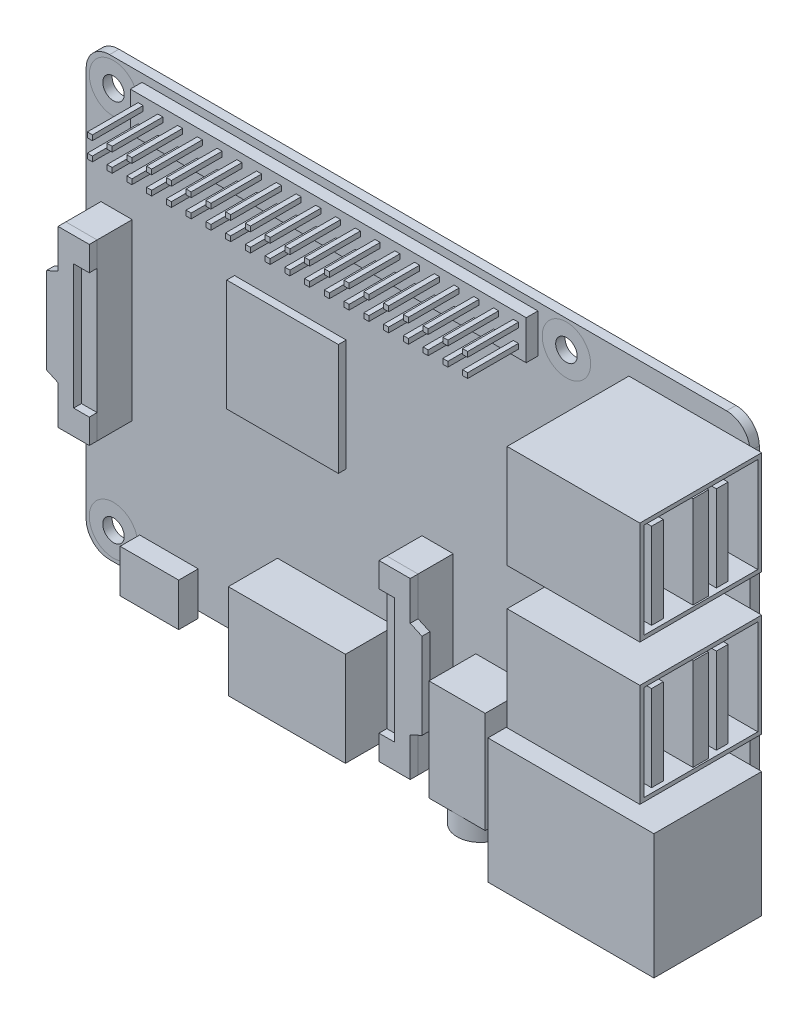
SolidWorks part; units mm, degrees
ref_plane "Ebene vorne" through (0, 0, 0) normal (0, 0, 1) x (1, 0, 0)
ref_plane "Ebene oben" through (0, 0, 0) normal (0, 1, 0) x (1, 0, 0)
ref_plane "Ebene rechts" through (0, 0, 0) normal (1, 0, 0) x (0, 0, -1)
sketch "Skizze1" plane through (0, 0, 0) normal (0, 0, 1) x (1, 0, 0)
  line L1 (42.5, -28) -> (-42.5, -28)
  line L2 (42.5, -28) -> (42.5, 28)
  line L3 (42.5, 28) -> (-42.5, 28)
  line L4 (-42.5, -28) -> (-42.5, 28)
  line L5 (42.5, -28) -> (-42.5, 28) construction
  line L6 (42.5, 28) -> (-42.5, -28) construction
  point P0 (0, 0)
  dimension "D1" = 85
  dimension "D2" = 56
extrude "Aufsatz-Linear austragen1" add sketch "Skizze1" along normal blind 1.2
fillet "Verrundung1" radius 3 4 edges at (-42.5, 28, 0.6) (-42.5, -28, 0.6) (42.5, -28, 0.6) (42.5, 28, 0.6)
sketch "Skizze2" plane through (0, 0, 1.2) normal (0, 0, 1) x (1, 0, 0)
  line L0 (-42.5, 25) -> (-42.5, -25) construction
  line L1 (39.5, 28) -> (-39.5, 28) construction
  line L2 (-39.5, -28) -> (39.5, -28) construction
  circle A0 centre (-39, 24.5) radius 1.375
  circle A1 centre (-39, -24.5) radius 1.375
  circle A2 centre (19, 24.5) radius 1.375
  circle A3 centre (19, -24.5) radius 1.375
  dimension "D4" = 2.75
  dimension "D1" = 3.5
  dimension "D2" = 3.5
  dimension "D3" = 3.5
  dimension "D5" = 58
extrude "Schnitt-Linear austragen1" cut sketch "Skizze2" against normal blind 5
sketch "Skizze3" plane through (0, 0, 1.2) normal (0, 0, 1) x (1, 0, 0)
  circle A0 centre (-39, 24.5) radius 3.1
  circle A1 centre (-39, -24.5) radius 3.1
  circle A2 centre (19, -24.5) radius 3.1
  circle A3 centre (19, 24.5) radius 3.1
  dimension "D1" = 6.2
split line "Trennlinie1"
sketch "Skizze4" plane through (0, 0, 1.2) normal (0, 0, 1) x (1, 0, 0)
  line L0 (-10.5, -28) -> (-10.5, -11.5436) construction
  line L1 (-40.6, 11.15) -> (-36.6, 11.15)
  line L2 (-40.6, 11.15) -> (-40.6, -11.15)
  line L3 (-40.6, -11.15) -> (-36.6, -11.15)
  line L4 (-36.6, 11.15) -> (-36.6, -11.15)
  line L5 (-40.6, 11.15) -> (-36.6, -11.15) construction
  line L6 (-40.6, -11.15) -> (-36.6, 11.15) construction
  line L7 (0.5, -5.35) -> (4.5, -5.35)
  line L8 (0.5, -5.35) -> (0.5, -27.65)
  line L9 (0.5, -27.65) -> (4.5, -27.65)
  line L10 (4.5, -5.35) -> (4.5, -27.65)
  line L11 (0.5, -5.35) -> (4.5, -27.65) construction
  line L12 (0.5, -27.65) -> (4.5, -5.35) construction
  line L13 (-39.5, -28) -> (39.5, -28) construction
  line L14 (-42.5, 25) -> (-42.5, -25) construction
  line L15 (2.5, -28) -> (2.5, -16.5) construction
  line L17 (-38.6, -8) -> (-34.6, -8)
  line L18 (-38.6, -8) -> (-38.6, 8)
  line L19 (-38.6, 8) -> (-34.6, 8)
  line L20 (-34.6, -8) -> (-34.6, 8)
  line L21 (-38.6, -8) -> (-34.6, 8) construction
  line L22 (-38.6, 8) -> (-34.6, -8) construction
  line L23 (2.5, -24.5) -> (-1.5, -24.5)
  line L24 (2.5, -24.5) -> (2.5, -8.5)
  line L25 (2.5, -8.5) -> (-1.5, -8.5)
  line L26 (-1.5, -24.5) -> (-1.5, -8.5)
  line L27 (2.5, -24.5) -> (-1.5, -8.5) construction
  line L28 (2.5, -8.5) -> (-1.5, -24.5) construction
  point P0 (-38.6, 0)
  point P5 (2.5, -16.5)
  point P18 (0.5, -16.5)
  point P19 (-36.6, 0)
  line M11 (-39.5, -28) -> (39.5, -28)
  dimension "D1" = 22.3
  dimension "D2" = 4
  dimension "D3" = 32
  dimension "D4" = 13
  dimension "D5" = 28
  dimension "D6" = 1.9
  dimension "D7" = 16
  dimension "D8" = 11.5
extrude "Aufsatz-Linear austragen2" add sketch "Skizze4" against normal blind 1 from offset 5.5 separate body contours L18 L19 L4 L1 L2 L3 L17 | L25 L24 L23 L8 L10 L7 M11
sketch "Skizze5" plane through (0, 0, 6.7) normal (0, 0, 1) x (1, 0, 0)
  line L0 (-36.6, 8) -> (-42.1, 5.5)
  line L1 (-42.1, 5.5) -> (-42.1, -5.5)
  line L2 (-42.1, -5.5) -> (-36.6, -8)
  line L3 (-42.1, 0) -> (-38.6, 0) construction
  line L4 (-38.6, -8) -> (-38.6, 8) construction
  line L6 (-40.6, 6.1818) -> (-40.6, -6.1818)
  line L7 (-40.6, 11.15) -> (-40.6, -11.15) construction
  line L8 (-42.1, 5.5) -> (-40.6, 5.5) construction
  line L9 (0.5, -8.5) -> (6, -11)
  line L10 (6, -11) -> (6, -22)
  line L11 (6, -22) -> (0.5, -24.5)
  line L12 (4.5, -10.3182) -> (4.5, -22.6818)
  line L13 (4.5, -5.35) -> (4.5, -27.65) construction
  line M14 (-40.6, 11.15) -> (-40.6, -11.15)
  dimension "D1" = 1.5
  dimension "D2" = 11
extrude "Aufsatz-Linear austragen3" add sketch "Skizze5" against normal up to vertex (1 mm away) contours L1 L2 L0 M14 | L9 L12 L11 L10 up to point (-40.6, 11.15, 5.7)
sketch "Skizze6" plane through (0, 0, 1.2) normal (0, 0, 1) x (1, 0, 0)
  line L1 (-40.6, 11.15) -> (-36.6, 11.15)
  line L2 (-40.6, 11.15) -> (-40.6, -11.15)
  line L3 (-40.6, -11.15) -> (-36.6, -11.15)
  line L4 (-36.6, 11.15) -> (-36.6, -11.15)
  line L5 (0.5, -5.35) -> (4.5, -5.35)
  line L6 (0.5, -5.35) -> (0.5, -27.65)
  line L7 (0.5, -27.65) -> (4.5, -27.65)
  line L8 (4.5, -5.35) -> (4.5, -27.65)
extrude "Aufsatz-Linear austragen4" add sketch "Skizze6" along normal up to vertex (4.5 mm away) separate body
sketch "Skizze7" plane through (0, 0, 1.2) normal (0, 0, 1) x (1, 0, 0)
  line L0 (-10, 27) -> (-10, 22) construction
  line L1 (-35.35, 27) -> (15.35, 27)
  line L2 (-35.35, 27) -> (-35.35, 22)
  line L3 (-35.35, 22) -> (15.35, 22)
  line L4 (15.35, 27) -> (15.35, 22)
  line L6 (39.5, 28) -> (-39.5, 28) construction
  circle A0 centre (-39, 24.5) radius 1.375 construction
  dimension "D3" = 29
  dimension "D1" = 50.7
  dimension "D2" = 5
  dimension "D4" = 1
extrude "Aufsatz-Linear austragen5" add sketch "Skizze7" along normal blind 1.5 separate body
sketch "Skizze8" plane through (0, 0, 2.7) normal (0, 0, 1) x (1, 0, 0)
  line L0 (-35.35, 24.5) -> (-33.4517, 24.5) construction
  line L1 (-34.35, 26) -> (-33.7, 26)
  line L2 (-34.35, 26) -> (-34.35, 25.35)
  line L3 (-34.35, 25.35) -> (-33.7, 25.35)
  line L4 (-33.7, 26) -> (-33.7, 25.35)
  line L5 (-34.35, 26) -> (-33.7, 25.35) construction
  line L6 (-34.35, 25.35) -> (-33.7, 26) construction
  line L7 (-35.35, 27) -> (-35.35, 22) construction
  line L8 (-34.025, 26) -> (-34.025, 27) construction
  line L9 (15.35, 27) -> (-35.35, 27) construction
  line L10 (-34.35, 25.675) -> (-35.35, 25.675) construction
  line L11 (-31.1711, 26) -> (-31.1711, 25.35)
  line L12 (-31.8211, 25.35) -> (-31.1711, 25.35)
  line L13 (-31.8211, 26) -> (-31.8211, 25.35)
  line L14 (-31.8211, 26) -> (-31.1711, 26)
  line L15 (-28.6421, 26) -> (-28.6421, 25.35)
  line L16 (-29.2921, 25.35) -> (-28.6421, 25.35)
  line L17 (-29.2921, 26) -> (-29.2921, 25.35)
  line L18 (-29.2921, 26) -> (-28.6421, 26)
  line L19 (-26.1132, 26) -> (-26.1132, 25.35)
  line L20 (-26.7632, 25.35) -> (-26.1132, 25.35)
  line L21 (-26.7632, 26) -> (-26.7632, 25.35)
  line L22 (-26.7632, 26) -> (-26.1132, 26)
  line L23 (-23.5842, 26) -> (-23.5842, 25.35)
  line L24 (-24.2342, 25.35) -> (-23.5842, 25.35)
  line L25 (-24.2342, 26) -> (-24.2342, 25.35)
  line L26 (-24.2342, 26) -> (-23.5842, 26)
  line L27 (-21.0553, 26) -> (-21.0553, 25.35)
  line L28 (-21.7053, 25.35) -> (-21.0553, 25.35)
  line L29 (-21.7053, 26) -> (-21.7053, 25.35)
  line L30 (-21.7053, 26) -> (-21.0553, 26)
  line L31 (-18.5263, 26) -> (-18.5263, 25.35)
  line L32 (-19.1763, 25.35) -> (-18.5263, 25.35)
  line L33 (-19.1763, 26) -> (-19.1763, 25.35)
  line L34 (-19.1763, 26) -> (-18.5263, 26)
  line L35 (-15.9974, 26) -> (-15.9974, 25.35)
  line L36 (-16.6474, 25.35) -> (-15.9974, 25.35)
  line L37 (-16.6474, 26) -> (-16.6474, 25.35)
  line L38 (-16.6474, 26) -> (-15.9974, 26)
  line L39 (-13.4684, 26) -> (-13.4684, 25.35)
  line L40 (-14.1184, 25.35) -> (-13.4684, 25.35)
  line L41 (-14.1184, 26) -> (-14.1184, 25.35)
  line L42 (-14.1184, 26) -> (-13.4684, 26)
  line L43 (-10.9395, 26) -> (-10.9395, 25.35)
  line L44 (-11.5895, 25.35) -> (-10.9395, 25.35)
  line L45 (-11.5895, 26) -> (-11.5895, 25.35)
  line L46 (-11.5895, 26) -> (-10.9395, 26)
  line L47 (-8.4105, 26) -> (-8.4105, 25.35)
  line L48 (-9.0605, 25.35) -> (-8.4105, 25.35)
  line L49 (-9.0605, 26) -> (-9.0605, 25.35)
  line L50 (-9.0605, 26) -> (-8.4105, 26)
  line L51 (-5.8816, 26) -> (-5.8816, 25.35)
  line L52 (-6.5316, 25.35) -> (-5.8816, 25.35)
  line L53 (-6.5316, 26) -> (-6.5316, 25.35)
  line L54 (-6.5316, 26) -> (-5.8816, 26)
  line L55 (-3.3526, 26) -> (-3.3526, 25.35)
  line L56 (-4.0026, 25.35) -> (-3.3526, 25.35)
  line L57 (-4.0026, 26) -> (-4.0026, 25.35)
  line L58 (-4.0026, 26) -> (-3.3526, 26)
  line L59 (-0.8237, 26) -> (-0.8237, 25.35)
  line L60 (-1.4737, 25.35) -> (-0.8237, 25.35)
  line L61 (-1.4737, 26) -> (-1.4737, 25.35)
  line L62 (-1.4737, 26) -> (-0.8237, 26)
  line L63 (1.7053, 26) -> (1.7053, 25.35)
  line L64 (1.0553, 25.35) -> (1.7053, 25.35)
  line L65 (1.0553, 26) -> (1.0553, 25.35)
  line L66 (1.0553, 26) -> (1.7053, 26)
  line L67 (4.2342, 26) -> (4.2342, 25.35)
  line L68 (3.5842, 25.35) -> (4.2342, 25.35)
  line L69 (3.5842, 26) -> (3.5842, 25.35)
  line L70 (3.5842, 26) -> (4.2342, 26)
  line L71 (6.7632, 26) -> (6.7632, 25.35)
  line L72 (6.1132, 25.35) -> (6.7632, 25.35)
  line L73 (6.1132, 26) -> (6.1132, 25.35)
  line L74 (6.1132, 26) -> (6.7632, 26)
  line L75 (9.2921, 26) -> (9.2921, 25.35)
  line L76 (8.6421, 25.35) -> (9.2921, 25.35)
  line L77 (8.6421, 26) -> (8.6421, 25.35)
  line L78 (8.6421, 26) -> (9.2921, 26)
  line L79 (11.8211, 26) -> (11.8211, 25.35)
  line L80 (11.1711, 25.35) -> (11.8211, 25.35)
  line L81 (11.1711, 26) -> (11.1711, 25.35)
  line L82 (11.1711, 26) -> (11.8211, 26)
  line L83 (14.35, 26) -> (14.35, 25.35)
  line L84 (13.7, 25.35) -> (14.35, 25.35)
  line L85 (13.7, 26) -> (13.7, 25.35)
  line L86 (13.7, 26) -> (14.35, 26)
  line L87 (14.35, 25.675) -> (15.35, 25.675) construction
  line L88 (15.35, 22) -> (15.35, 27) construction
  line L89 (-34.025, 23) -> (-34.025, 22) construction
  line L90 (-34.35, 23.65) -> (-33.7, 23) construction
  line L91 (-34.35, 23) -> (-33.7, 23.65) construction
  line L92 (13.7, 23) -> (14.35, 23)
  line L93 (13.7, 23) -> (13.7, 23.65)
  line L94 (13.7, 23.65) -> (14.35, 23.65)
  line L95 (14.35, 23) -> (14.35, 23.65)
  line L96 (11.1711, 23) -> (11.8211, 23)
  line L97 (11.1711, 23) -> (11.1711, 23.65)
  line L98 (11.1711, 23.65) -> (11.8211, 23.65)
  line L99 (11.8211, 23) -> (11.8211, 23.65)
  line L100 (8.6421, 23) -> (9.2921, 23)
  line L101 (8.6421, 23) -> (8.6421, 23.65)
  line L102 (8.6421, 23.65) -> (9.2921, 23.65)
  line L103 (9.2921, 23) -> (9.2921, 23.65)
  line L104 (6.1132, 23) -> (6.7632, 23)
  line L105 (6.1132, 23) -> (6.1132, 23.65)
  line L106 (6.1132, 23.65) -> (6.7632, 23.65)
  line L107 (6.7632, 23) -> (6.7632, 23.65)
  line L108 (3.5842, 23) -> (4.2342, 23)
  line L109 (3.5842, 23) -> (3.5842, 23.65)
  line L110 (3.5842, 23.65) -> (4.2342, 23.65)
  line L111 (4.2342, 23) -> (4.2342, 23.65)
  line L112 (1.0553, 23) -> (1.7053, 23)
  line L113 (1.0553, 23) -> (1.0553, 23.65)
  line L114 (1.0553, 23.65) -> (1.7053, 23.65)
  line L115 (1.7053, 23) -> (1.7053, 23.65)
  line L116 (-1.4737, 23) -> (-0.8237, 23)
  line L117 (-1.4737, 23) -> (-1.4737, 23.65)
  line L118 (-1.4737, 23.65) -> (-0.8237, 23.65)
  line L119 (-0.8237, 23) -> (-0.8237, 23.65)
  line L120 (-4.0026, 23) -> (-3.3526, 23)
  line L121 (-4.0026, 23) -> (-4.0026, 23.65)
  line L122 (-4.0026, 23.65) -> (-3.3526, 23.65)
  line L123 (-3.3526, 23) -> (-3.3526, 23.65)
  line L124 (-6.5316, 23) -> (-5.8816, 23)
  line L125 (-6.5316, 23) -> (-6.5316, 23.65)
  line L126 (-6.5316, 23.65) -> (-5.8816, 23.65)
  line L127 (-5.8816, 23) -> (-5.8816, 23.65)
  line L128 (-9.0605, 23) -> (-8.4105, 23)
  line L129 (-9.0605, 23) -> (-9.0605, 23.65)
  line L130 (-9.0605, 23.65) -> (-8.4105, 23.65)
  line L131 (-8.4105, 23) -> (-8.4105, 23.65)
  line L132 (-11.5895, 23) -> (-10.9395, 23)
  line L133 (-11.5895, 23) -> (-11.5895, 23.65)
  line L134 (-11.5895, 23.65) -> (-10.9395, 23.65)
  line L135 (-10.9395, 23) -> (-10.9395, 23.65)
  line L136 (-14.1184, 23) -> (-13.4684, 23)
  line L137 (-14.1184, 23) -> (-14.1184, 23.65)
  line L138 (-14.1184, 23.65) -> (-13.4684, 23.65)
  line L139 (-13.4684, 23) -> (-13.4684, 23.65)
  line L140 (-16.6474, 23) -> (-15.9974, 23)
  line L141 (-16.6474, 23) -> (-16.6474, 23.65)
  line L142 (-16.6474, 23.65) -> (-15.9974, 23.65)
  line L143 (-15.9974, 23) -> (-15.9974, 23.65)
  line L144 (-19.1763, 23) -> (-18.5263, 23)
  line L145 (-19.1763, 23) -> (-19.1763, 23.65)
  line L146 (-19.1763, 23.65) -> (-18.5263, 23.65)
  line L147 (-18.5263, 23) -> (-18.5263, 23.65)
  line L148 (-21.7053, 23) -> (-21.0553, 23)
  line L149 (-21.7053, 23) -> (-21.7053, 23.65)
  line L150 (-21.7053, 23.65) -> (-21.0553, 23.65)
  line L151 (-21.0553, 23) -> (-21.0553, 23.65)
  line L152 (-24.2342, 23) -> (-23.5842, 23)
  line L153 (-24.2342, 23) -> (-24.2342, 23.65)
  line L154 (-24.2342, 23.65) -> (-23.5842, 23.65)
  line L155 (-23.5842, 23) -> (-23.5842, 23.65)
  line L156 (-26.7632, 23) -> (-26.1132, 23)
  line L157 (-26.7632, 23) -> (-26.7632, 23.65)
  line L158 (-26.7632, 23.65) -> (-26.1132, 23.65)
  line L159 (-26.1132, 23) -> (-26.1132, 23.65)
  line L160 (-29.2921, 23) -> (-28.6421, 23)
  line L161 (-29.2921, 23) -> (-29.2921, 23.65)
  line L162 (-29.2921, 23.65) -> (-28.6421, 23.65)
  line L163 (-28.6421, 23) -> (-28.6421, 23.65)
  line L164 (-31.8211, 23) -> (-31.1711, 23)
  line L165 (-31.8211, 23) -> (-31.8211, 23.65)
  line L166 (-31.8211, 23.65) -> (-31.1711, 23.65)
  line L167 (-31.1711, 23) -> (-31.1711, 23.65)
  line L168 (-33.7, 23) -> (-33.7, 23.65)
  line L169 (-34.35, 23.65) -> (-33.7, 23.65)
  line L170 (-34.35, 23) -> (-34.35, 23.65)
  line L171 (-34.35, 23) -> (-33.7, 23)
  point P0 (-34.025, 25.675)
  point P177 (-34.025, 23.325)
  dimension "D1" = 0.65
  dimension "D2" = 1
  dimension "D3" = 20
extrude "Aufsatz-Linear austragen6" add sketch "Skizze8" along normal blind 6.5
sketch "Skizze10" plane through (0, 0, 1.2) normal (0, 0, 1) x (1, 0, 0)
  line L0 (44, -17.75) -> (22.75, -17.75) construction
  line L1 (27, 25.6) -> (44, 25.6)
  line L2 (27, 25.6) -> (27, 12.4)
  line L3 (27, 12.4) -> (44, 12.4)
  line L4 (44, 25.6) -> (44, 12.4)
  line L5 (27, 7.6) -> (44, 7.6)
  line L6 (27, 7.6) -> (27, -5.6)
  line L7 (27, -5.6) -> (44, -5.6)
  line L8 (44, 7.6) -> (44, -5.6)
  line L9 (22.75, -9.75) -> (44, -9.75)
  line L10 (22.75, -9.75) -> (22.75, -25.75)
  line L11 (22.75, -25.75) -> (44, -25.75)
  line L12 (44, -9.75) -> (44, -25.75)
  line L13 (27, 1) -> (44, 1) construction
  line L14 (27, 19) -> (44, 19) construction
  line L15 (-39.5, -28) -> (39.5, -28) construction
  line L16 (42.5, -25) -> (42.5, 25) construction
  line L17 (-10.5, -29.2) -> (-10.5, -17.1) construction
  line L18 (-18, -17.1) -> (-3, -17.1)
  line L19 (-18, -17.1) -> (-18, -29.2)
  line L20 (-18, -29.2) -> (-3, -29.2)
  line L21 (-3, -17.1) -> (-3, -29.2)
  line L22 (-42.5, 25) -> (-42.5, -25) construction
  line L23 (11, -28) -> (11, -15) construction
  line L24 (7.4, -15) -> (14.6, -15)
  line L25 (7.4, -15) -> (7.4, -28)
  line L26 (7.4, -28) -> (14.6, -28)
  line L27 (14.6, -15) -> (14.6, -28)
  line L28 (-31.9, -28.85) -> (-31.9, -23.35) construction
  line L29 (-35.65, -23.35) -> (-28.15, -23.35)
  line L30 (-35.65, -23.35) -> (-35.65, -28.85)
  line L31 (-35.65, -28.85) -> (-28.15, -28.85)
  line L32 (-28.15, -23.35) -> (-28.15, -28.85)
  line L34 (-41.5, 6) -> (-30, 6)
  line L35 (-41.5, 6) -> (-41.5, -6)
  line L36 (-41.5, -6) -> (-30, -6)
  line L37 (-30, 6) -> (-30, -6)
  point P46 (-30, 0)
  dimension "D1" = 10.25
  dimension "D2" = 1.5
  dimension "D3" = 21.25
  dimension "D4" = 17
  dimension "D5" = 16
  dimension "D6" = 13.2
  dimension "D7" = 29
  dimension "D8" = 47
  dimension "D9" = 32
  dimension "D10" = 15
  dimension "D11" = 12.1
  dimension "D12" = 1.2
  dimension "D13" = 53.5
  dimension "D14" = 7.2
  dimension "D15" = 13
  dimension "D16" = 7.5
  dimension "D17" = 5.5
  dimension "D18" = 0.85
  dimension "D19" = 10.6
  dimension "D20" = 12
  dimension "D21" = 11.5
  dimension "D22" = 1
sketch "Skizze11" plane through (0, 0, 0) normal (0, 0, -1) x (-1, 0, 0)
  line L0 (41.5, 6) -> (41.5, -6) construction
  line L1 (41.5, -6) -> (30, -6) construction
  line L2 (30, 6) -> (30, -6) construction
  line L3 (41.5, 6) -> (30, 6) construction
  line L4 (41.5, 6) -> (41.5, -6)
  line L5 (41.5, -6) -> (30, -6)
  line L6 (30, 6) -> (30, -6)
  line L7 (41.5, 6) -> (30, 6)
extrude "Aufsatz-Linear austragen7" add sketch "Skizze11" along normal blind 2 separate body
sketch "Skizze12" plane through (0, 0, 1.2) normal (0, 0, 1) x (1, 0, 0)
  line L0 (-35.65, -23.35) -> (-28.15, -23.35) construction
  line L1 (-35.65, -23.35) -> (-35.65, -28.85) construction
  line L2 (-35.65, -28.85) -> (-28.15, -28.85) construction
  line L3 (-28.15, -23.35) -> (-28.15, -28.85) construction
  line L4 (-35.65, -23.35) -> (-28.15, -23.35)
  line L5 (-35.65, -23.35) -> (-35.65, -28.85)
  line L6 (-35.65, -28.85) -> (-28.15, -28.85)
  line L7 (-28.15, -23.35) -> (-28.15, -28.85)
extrude "Aufsatz-Linear austragen8" add sketch "Skizze12" along normal blind 2.5 separate body
sketch "Skizze13" plane through (0, 0, 1.2) normal (0, 0, 1) x (1, 0, 0)
  line L0 (-18, -17.1) -> (-18, -29.2) construction
  line L1 (-18, -29.2) -> (-3, -29.2) construction
  line L2 (-3, -17.1) -> (-3, -29.2) construction
  line L3 (-18, -17.1) -> (-3, -17.1) construction
  line L4 (-18, -17.1) -> (-18, -29.2)
  line L5 (-18, -29.2) -> (-3, -29.2)
  line L6 (-3, -17.1) -> (-3, -29.2)
  line L7 (-18, -17.1) -> (-3, -17.1)
extrude "Aufsatz-Linear austragen9" add sketch "Skizze13" along normal blind 6.3 separate body
sketch "Skizze14" plane through (0, 0, 1.2) normal (0, 0, 1) x (1, 0, 0)
  line L0 (7.4, -15) -> (14.6, -15) construction
  line L1 (7.4, -15) -> (7.4, -28) construction
  line L2 (7.4, -28) -> (14.6, -28) construction
  line L3 (14.6, -15) -> (14.6, -28) construction
  line L4 (7.4, -15) -> (14.6, -15)
  line L5 (7.4, -15) -> (7.4, -28)
  line L6 (7.4, -28) -> (14.6, -28)
  line L7 (14.6, -15) -> (14.6, -28)
extrude "Aufsatz-Linear austragen10" add sketch "Skizze14" along normal blind 6 separate body
sketch "Skizze15" plane through (0, -28, 0) normal (0, -1, 0) x (1, 0, 0)
  line L0 (7.4, 7.2) -> (14.6, 7.2) construction
  line L1 (14.6, 7.2) -> (14.6, 1.2) construction
  circle A0 centre (11, 4.2) radius 3
  point P4 (11, 7.2)
  point P7 (14.6, 4.2)
  dimension "D1" = 6
extrude "Aufsatz-Linear austragen11" add sketch "Skizze15" along normal blind 2.5 contours A0
sketch "Skizze16" plane through (0, 0, 1.2) normal (0, 0, 1) x (1, 0, 0)
  line L0 (22.75, -9.75) -> (22.75, -25.75) construction
  line L1 (22.75, -25.75) -> (44, -25.75) construction
  line L2 (44, -9.75) -> (44, -25.75) construction
  line L3 (22.75, -9.75) -> (44, -9.75) construction
  line L4 (22.75, -9.75) -> (22.75, -25.75)
  line L5 (22.75, -25.75) -> (44, -25.75)
  line L6 (44, -9.75) -> (44, -25.75)
  line L7 (22.75, -9.75) -> (44, -9.75)
extrude "Aufsatz-Linear austragen12" add sketch "Skizze16" along normal blind 13.8 separate body
sketch "Skizze17" plane through (0, 0, 1.2) normal (0, 0, 1) x (1, 0, 0)
  line L0 (27, 25.6) -> (27, 12.4) construction
  line L1 (27, 25.6) -> (44, 25.6) construction
  line L2 (44, 25.6) -> (44, 12.4) construction
  line L3 (27, 12.4) -> (44, 12.4) construction
  line L4 (27, 7.6) -> (27, -5.6) construction
  line L5 (27, -5.6) -> (44, -5.6) construction
  line L6 (44, 7.6) -> (44, -5.6) construction
  line L7 (27, 7.6) -> (44, 7.6) construction
  line L8 (27, 25.6) -> (27, 12.4) construction
  line L9 (27, 25.6) -> (44, 25.6) construction
  line L10 (44, 25.6) -> (44, 12.4) construction
  line L11 (27, 12.4) -> (44, 12.4) construction
  line L12 (27, 7.6) -> (27, -5.6)
  line L13 (27, -5.6) -> (44, -5.6)
  line L14 (44, 7.6) -> (44, -5.6)
  line L15 (27, 7.6) -> (44, 7.6)
extrude "Aufsatz-Linear austragen13" add sketch "Skizze17" along normal blind 15.6 separate body
shell "Schale1" thickness 0.5
sketch "Skizze18" plane through (44, 0, 0) normal (1, 0, 0) x (0, 0, -1)
  line L0 (-9, -4.9) -> (-9, -5.1) construction
  line L1 (-10, 6.9) -> (-8, 6.9)
  line L2 (-10, 6.9) -> (-10, -4.9)
  line L3 (-10, -4.9) -> (-8, -4.9)
  line L4 (-8, 6.9) -> (-8, -4.9)
  line L5 (-16.3, -5.1) -> (-1.7, -5.1) construction
  line L6 (-9, 7.1) -> (-9, 6.9) construction
  line L7 (-16.3, 7.1) -> (-1.7, 7.1) construction
  line L8 (-16.3, 7.1) -> (-1.7, 7.1) construction
  dimension "D1" = 0.2
  dimension "D2" = 2
extrude "Aufsatz-Linear austragen14" add sketch "Skizze18" against normal up to vertex (16.5 mm away) up to point (27.5, -5.1, 1.7)
sketch "Skizze19" plane through (27.5, 0, 0) normal (1, 0, 0) x (0, 0, -1)
  line L0 (-16.3, -5.1) -> (-16.3, 7.1) construction
  line L1 (-15.3, 6.5) -> (-13.8, 6.5)
  line L2 (-15.3, 6.5) -> (-15.3, -4.5)
  line L3 (-15.3, -4.5) -> (-13.8, -4.5)
  line L4 (-13.8, 6.5) -> (-13.8, -4.5)
  line L5 (-10, 6.9) -> (-10, -4.9) construction
  line L6 (-13.8, 1) -> (-10, 1) construction
  line L7 (-8, -4.9) -> (-8, 6.9) construction
  line L8 (-7, 6.5) -> (-5.5, 6.5)
  line L9 (-7, 6.5) -> (-7, -4.5)
  line L10 (-7, -4.5) -> (-5.5, -4.5)
  line L11 (-5.5, 6.5) -> (-5.5, -4.5)
  dimension "D1" = 1
  dimension "D2" = 1.5
  dimension "D3" = 11
  dimension "D4" = 1
extrude "Aufsatz-Linear austragen15" add sketch "Skizze19" along normal up to vertex (16.5 mm away) separate body up to point (44, 6.9, 10)
pattern_linear "Lineares Muster1" count 2 spacing 18 along (0, 1, 0) of bodies 163 164 162
sketch "Skizze20" plane through (0, 0, 1.2) normal (0, 0, 1) x (1, 0, 0)
  line L0 (-42.5, 25) -> (-42.5, -25) construction
  line L1 (-23.5, 11.5) -> (-9.2, 11.5)
  line L2 (-23.5, 11.5) -> (-23.5, -2.8)
  line L3 (-23.5, -2.8) -> (-9.2, -2.8)
  line L4 (-9.2, 11.5) -> (-9.2, -2.8)
  line L5 (39.5, 28) -> (-39.5, 28) construction
  dimension "D1" = 19
  dimension "D2" = 16.5
  dimension "D3" = 14.3
extrude "Aufsatz-Linear austragen16" add sketch "Skizze20" along normal blind 1 separate body
equation "\"D2@Skizze2\"=\"D1@Skizze2\""
equation "\"D3@Skizze2\"=\"D1@Skizze2\""
equation "\"D4@Skizze19\"=\"D1@Skizze19\""
